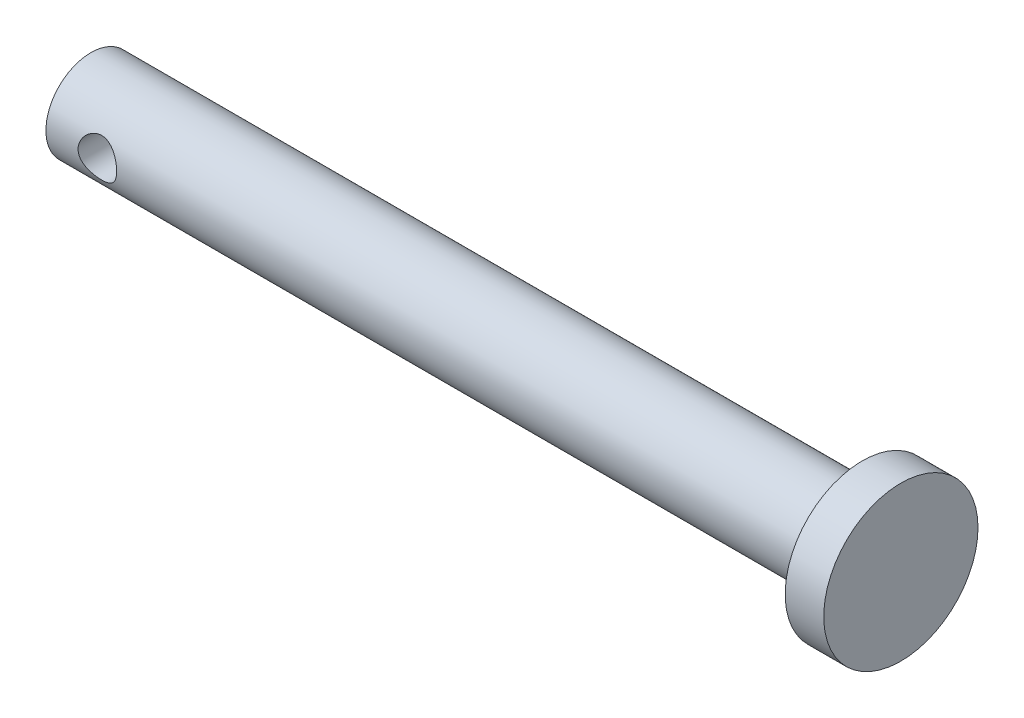
SolidWorks part; units mm, degrees
ref_plane "Front Plane" through (0, 0, 0) normal (0, 0, 1) x (1, 0, 0)
ref_plane "Top Plane" through (0, 0, 0) normal (0, 1, 0) x (1, 0, 0)
ref_plane "Right Plane" through (0, 0, 0) normal (1, 0, 0) x (0, 0, -1)
sketch "Sketch1" plane through (0, 0, 0) normal (1, 0, 0) x (0, 0, -1)
  circle A0 centre (0, 0) radius 3.5
  dimension "D1" = 7
extrude "Boss-Extrude1" add sketch "Sketch1" along normal blind 60
sketch "Sketch2" plane through (60, 0, 0) normal (1, 0, 0) x (0, 0, -1)
  circle A0 centre (0, 0) radius 6
  dimension "D1" = 12
extrude "Boss-Extrude2" add sketch "Sketch2" along normal blind 3
sketch "Sketch3" plane through (0, 0, 0) normal (0, 0, 1) x (1, 0, 0)
  line L0 (6.6, 0) -> (-6.6, 0) construction
  line L1 (0, -6.6) -> (0, 6.6) construction
  circle A0 centre (4, 0) radius 1.5
  dimension "D1" = 3
  dimension "D2" = 4
extrude "Cut-Extrude1" cut sketch "Sketch3" against normal through all both and the other way through all
chamfer "Chamfer1" [suppressed] distance 0.5 angle 45
sketch "Sketch4" plane through (0, 0, 0) normal (-1, 0, 0) x (0, 0, 1)
  circle A0 centre (0, 0) radius 6
extrude "Boss-Extrude3" [suppressed] add sketch "Sketch4" along normal blind 3
chamfer "Chamfer2" [suppressed] distance 0.5 angle 45
